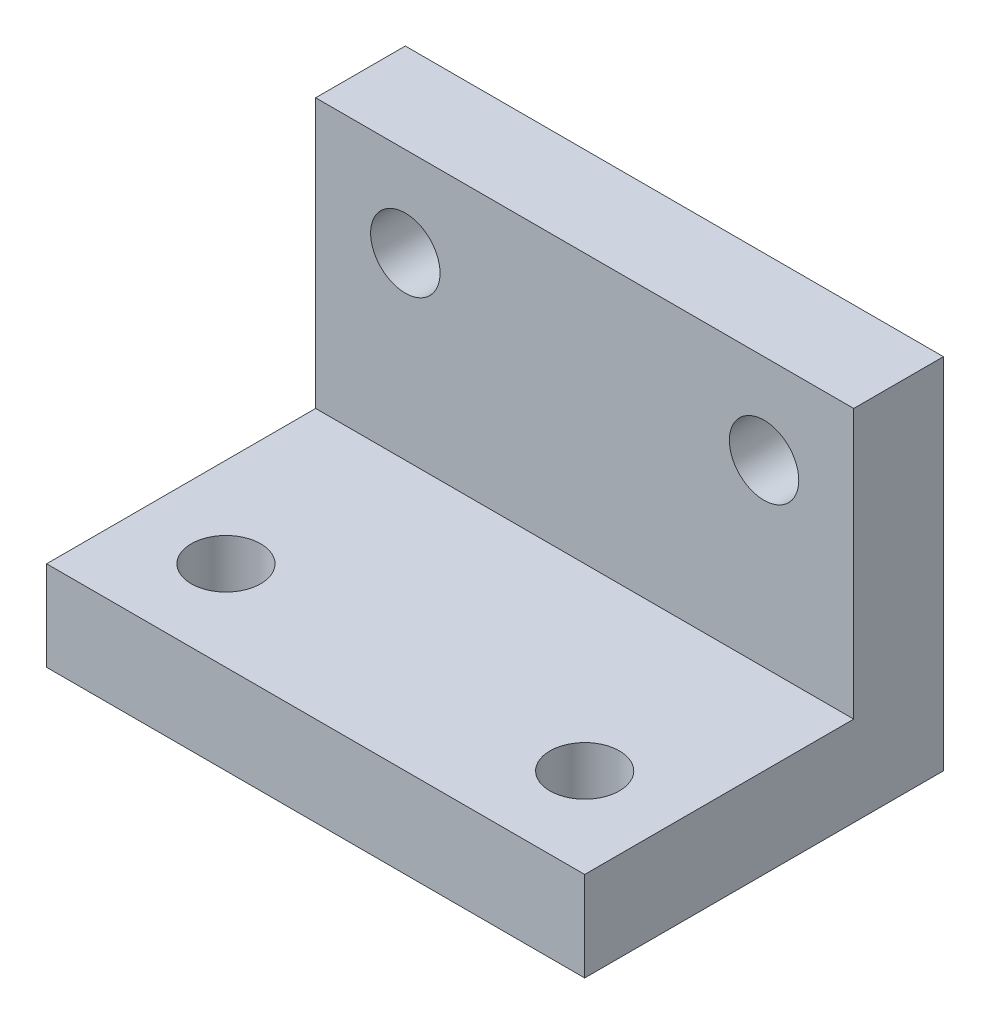
SolidWorks part; units mm, degrees
material "6061 Alloy"
ref_plane "Front Plane" through (0, 0, 0) normal (0, 0, 1) x (1, 0, 0)
ref_plane "Top Plane" through (0, 0, 0) normal (0, 1, 0) x (1, 0, 0)
ref_plane "Right Plane" through (0, 0, 0) normal (1, 0, 0) x (0, 0, -1)
sketch "Sketch1" plane through (0, 0, 0) normal (0, 1, 0) x (1, 0, 0)
  line L1 (-19.05, 12.7) -> (19.05, 12.7)
  line L2 (-19.05, 12.7) -> (-19.05, -12.7)
  line L3 (-19.05, -12.7) -> (19.05, -12.7)
  line L4 (19.05, 12.7) -> (19.05, -12.7)
  dimension "D1" = 19.05
  dimension "D2" = 19.05
  dimension "D3" = 12.7
  dimension "D4" = 12.7
extrude "Boss-Extrude1" add sketch "Sketch1" along normal mid plane 25.4
sketch "Sketch2" plane through (19.05, 0, 0) normal (1, 0, 0) x (0, 0, -1)
  line L0 (12.7, 12.7) -> (12.7, -12.7) construction
  line L1 (-12.7, 12.7) -> (6.35, 12.7)
  line L2 (-12.7, 12.7) -> (-12.7, -6.35)
  line L3 (-12.7, -6.35) -> (6.35, -6.35)
  line L4 (6.35, 12.7) -> (6.35, -6.35)
  line L5 (-12.7, -12.7) -> (12.7, -12.7) construction
  dimension "D1" = 6.35
  dimension "D2" = 6.35
extrude "Cut-Extrude1" cut sketch "Sketch2" against normal up to next
hole_wizard "#10 (0.1935) Diameter Hole2" positions "Sketch4" profile "Sketch3" hole size "#10" standard "ANSI Inch" end condition up to next
sketch "Sketch4" plane through (0, 0, -6.35) normal (0, 0, 1) x (1, 0, 0)
  line L0 (-19.05, -6.35) -> (19.05, -6.35) construction
  point P0 (-12.7, 6.35)
  point P2 (12.7, 6.35)
  dimension "D1" = 12.7
  dimension "D2" = 12.7
  dimension "D3" = 12.7
sketch "Sketch3" plane through (-12.7, 6.35, -6.35) normal (1, 0, 0) x (0, -1, 0)
  line L0 (0, 0) -> (0, 6.35)
  line L1 (0, 6.35) -> (2.4574, 6.35)
  line L2 (2.4574, 6.35) -> (2.4574, 0)
  line L5 (2.4574, 0) -> (0, 0)
  line L11 (0, -6.35) -> (0, 107.95) construction
  dimension "Thru Hole Dia." = 4.9149
  dimension "Thru Hole Depth" = 6.35
hole_wizard "#10 (0.1935) Diameter Hole1" positions "Sketch6" profile "Sketch5" hole size "#10" standard "ANSI Inch"
sketch "Sketch6" plane through (0, -6.35, 0) normal (0, 1, 0) x (1, 0, 0)
  line L0 (-19.05, 6.35) -> (19.05, 6.35) construction
  point P0 (-12.7, -6.35)
  point P2 (12.7, -6.35)
  dimension "D1" = 12.7
  dimension "D2" = 12.7
  dimension "D3" = 12.7
sketch "Sketch5" plane through (-12.7, -6.35, 6.35) normal (1, 0, 0) x (0, 0, 1)
  line L0 (0, 0) -> (0, 14.1766)
  line L1 (0, 14.1766) -> (2.4574, 12.7)
  line L2 (2.4574, 12.7) -> (2.4574, 0)
  line L5 (2.4574, 0) -> (0, 0)
  line L10 (0, 14.1766) -> (-2.4575, 12.7) construction
  line L11 (0, -6.35) -> (0, 107.95) construction
  dimension "Hole Dia." = 4.9149
  dimension "Hole Depth" = 12.7
  dimension "Drill Angle" = 118
